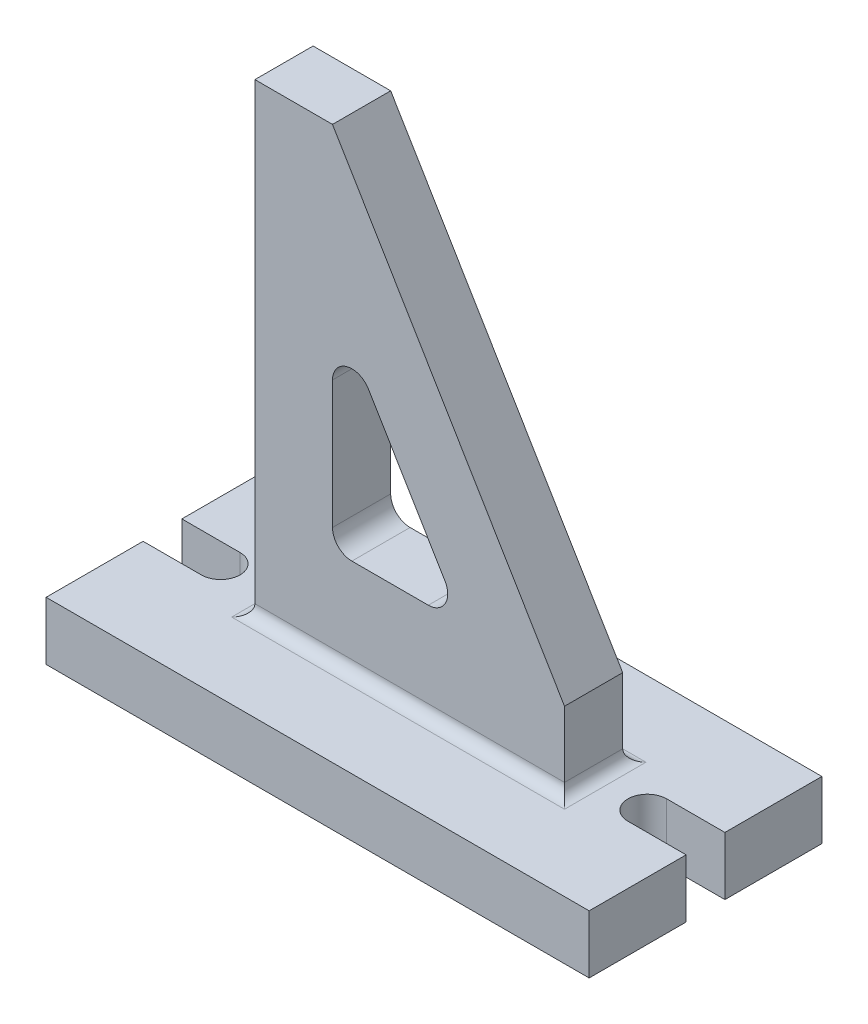
SolidWorks part; units mm, degrees
ref_plane "Front Plane" through (0, 0, 0) normal (0, 0, 1) x (1, 0, 0)
ref_plane "Top Plane" through (0, 0, 0) normal (0, 1, 0) x (1, 0, 0)
ref_plane "Right Plane" through (0, 0, 0) normal (1, 0, 0) x (0, 0, -1)
sketch "Sketch1" plane through (0, 0, 0) normal (0, 1, 0) x (1, 0, 0)
  line L1 (-76.2, 38.1) -> (101.6, 38.1)
  line L2 (-76.2, 38.1) -> (-76.2, -38.1)
  line L3 (-76.2, -38.1) -> (101.6, -38.1)
  line L4 (101.6, 38.1) -> (101.6, -38.1)
  dimension "D1" = 76.2
  dimension "D2" = 177.8
  dimension "D3" = 76.2
  dimension "D4" = 38.1
extrude "Milling Support Base" add sketch "Sketch1" against normal blind 19.05
sketch "Sketch2" plane through (0, 0, 0) normal (0, 1, 0) x (1, 0, 0)
  line L0 (-76.2, 38.1) -> (-76.2, -38.1) construction
  line L2 (-76.2, 6.35) -> (-57.15, 6.35)
  line L4 (-76.2, 6.35) -> (-76.2, -6.35)
  line L5 (-76.2, -6.35) -> (-57.15, -6.35)
  line L7 (-76.2, -38.1) -> (101.6, -38.1) construction
  arc A0 (-57.15, 6.35) -> (-57.15, -6.35) centre (-57.15, 0) cw
  dimension "D3" = 19.05
  dimension "D1" = 38.1
  dimension "D2" = 6.35
extrude "Bolt Slot Left End" cut sketch "Sketch2" against normal through all
sketch "Sketch3" plane through (0, -19.05, 0) normal (0, -1, 0) x (1, 0, 0)
  line L0 (101.6, 38.1) -> (101.6, -38.1) construction
  line L1 (101.6, 6.35) -> (82.55, 6.35)
  line L2 (101.6, 6.35) -> (101.6, -6.35)
  line L3 (101.6, -6.35) -> (82.55, -6.35)
  line L5 (101.6, -38.1) -> (-76.2, -38.1) construction
  arc A0 (82.55, 6.35) -> (82.55, -6.35) centre (82.55, 0) ccw
  dimension "D1" = 19.05
  dimension "D2" = 12.7
  dimension "D3" = 38.1
extrude "Bolt Slot Right End" cut sketch "Sketch3" against normal through all
sketch "Sketch4" plane through (0, 0, 0) normal (0, 0, 1) x (1, 0, 0)
  line L0 (-36.4086, 0) -> (-36.4086, 152.4)
  line L1 (-76.2, 0) -> (101.6, 0) construction
  line L2 (-36.4086, 152.4) -> (-11.0086, 152.4)
  line L3 (64.9592, 0) -> (64.9592, 25.4)
  line L4 (64.9592, 25.4) -> (-11.0086, 152.4)
  line L5 (64.9592, 0) -> (-36.4086, 0)
  dimension "D1" = 152.4
  dimension "D2" = 25.4
  dimension "D3" = 25.4
extrude "Outer Triangle" add sketch "Sketch4" along normal mid plane 19.05
sketch "Sketch5" plane through (0, 0, 9.525) normal (0, 0, 1) x (1, 0, 0)
  line L0 (-4.6586, 31.75) -> (20.3657, 31.75)
  line L1 (25.8152, 41.3597) -> (0.7909, 83.1944)
  line L2 (-11.0086, 79.9347) -> (-11.0086, 38.1)
  line L3 (-36.4086, 0) -> (64.9592, 0) construction
  line L5 (-36.4086, 152.4) -> (-36.4086, 0) construction
  line L6 (64.9592, 25.4) -> (-11.0086, 152.4) construction
  arc A0 (25.8152, 41.3597) -> (20.3657, 31.75) centre (20.3657, 38.1) cw
  arc A1 (-4.6586, 31.75) -> (-11.0086, 38.1) centre (-4.6586, 38.1) cw
  arc A2 (0.7909, 83.1944) -> (-11.0086, 79.9347) centre (-4.6586, 79.9347) ccw
  dimension "D4" = 6.35
  dimension "D1" = 31.75
  dimension "D2" = 25.4
  dimension "D3" = 25.4
extrude "Inner Triangle" cut sketch "Sketch5" against normal through all
ref_plane "Plane1" through (-41.4886, 0, 0) normal (-1, 0, 0) x (0, 0, 1)
sketch "Sketch6" plane through (-41.4886, 0, 0) normal (-1, 0, 0) x (0, 0, 1)
  line L0 (9.525, 152.4) -> (9.525, 0) construction
  line L1 (-9.525, 152.4) -> (9.525, 152.4)
  line L2 (-9.525, 152.4) -> (-9.525, 76.2)
  line L3 (-9.525, 76.2) -> (9.525, 76.2)
  line L4 (9.525, 152.4) -> (9.525, 76.2)
  dimension "D1" = 76.2
split line "Split Line1"
fillet "Fillet at Triangle base" radius 3.81 4 edges at (14.2753, 0, 9.525) (14.2753, 0, -9.525) (64.9592, 0, 0) (-36.4086, 0, 0)
